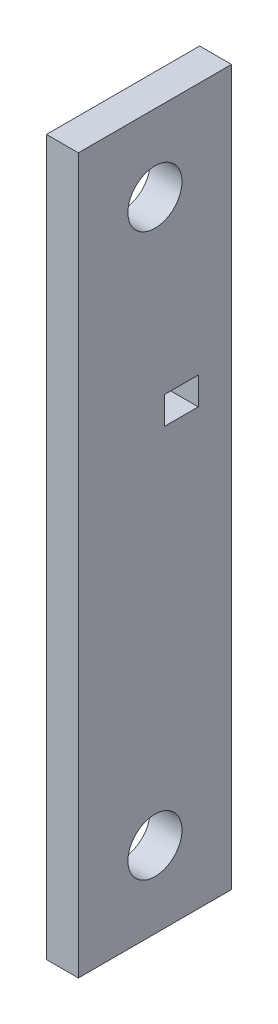
SolidWorks part; units mm, degrees
material "ASTM A36"
ref_plane "Front" through (0, 0, 0) normal (0, 0, 1) x (1, 0, 0)
ref_plane "Top" through (0, 0, 0) normal (0, 1, 0) x (1, 0, 0)
ref_plane "Side" through (0, 0, 0) normal (1, 0, 0) x (0, 0, -1)
sketch "Sketch1" plane through (0, 0, 0) normal (0, 0, 1) x (1, 0, 0)
  line L0 (0, -88.9) -> (0, 88.9)
  dimension "D1" = 177.8
extrude "Extrude-Thin1" add sketch "Sketch1" along normal mid plane 38.1 thin thin type mid plane wall 7.9375
sketch "Sketch2" plane through (0, 0, 0) normal (1, 0, 0) x (0, 0, -1)
  line L0 (-19.05, -88.9) -> (19.05, -88.9) construction
  circle A0 centre (0, 69.85) radius 6.731
  circle A1 centre (0, -69.85) radius 6.731
  dimension "D1" = 13.462
  dimension "D2" = 139.7
  dimension "D3" = 19.05
extrude "Cut-Extrude1" cut sketch "Sketch2" against normal blind 5.08 and the other way through all
sketch "Sketch3" plane through (0, 0, 0) normal (1, 0, 0) x (0, 0, -1)
  line L0 (2.3952, 19.2532) -> (10.7772, 19.2532)
  line L1 (10.7772, 19.2532) -> (10.7772, 26.1112)
  line L2 (10.7772, 26.1112) -> (2.3952, 26.1112)
  line L3 (2.3952, 26.1112) -> (2.3952, 19.2532)
  dimension "D1" = 19.2532
  dimension "D2" = 8.382
  dimension "D3" = 2.3952
  dimension "D4" = 6.858
extrude "Cut-Extrude2" cut sketch "Sketch3" against normal through all and the other way through all
